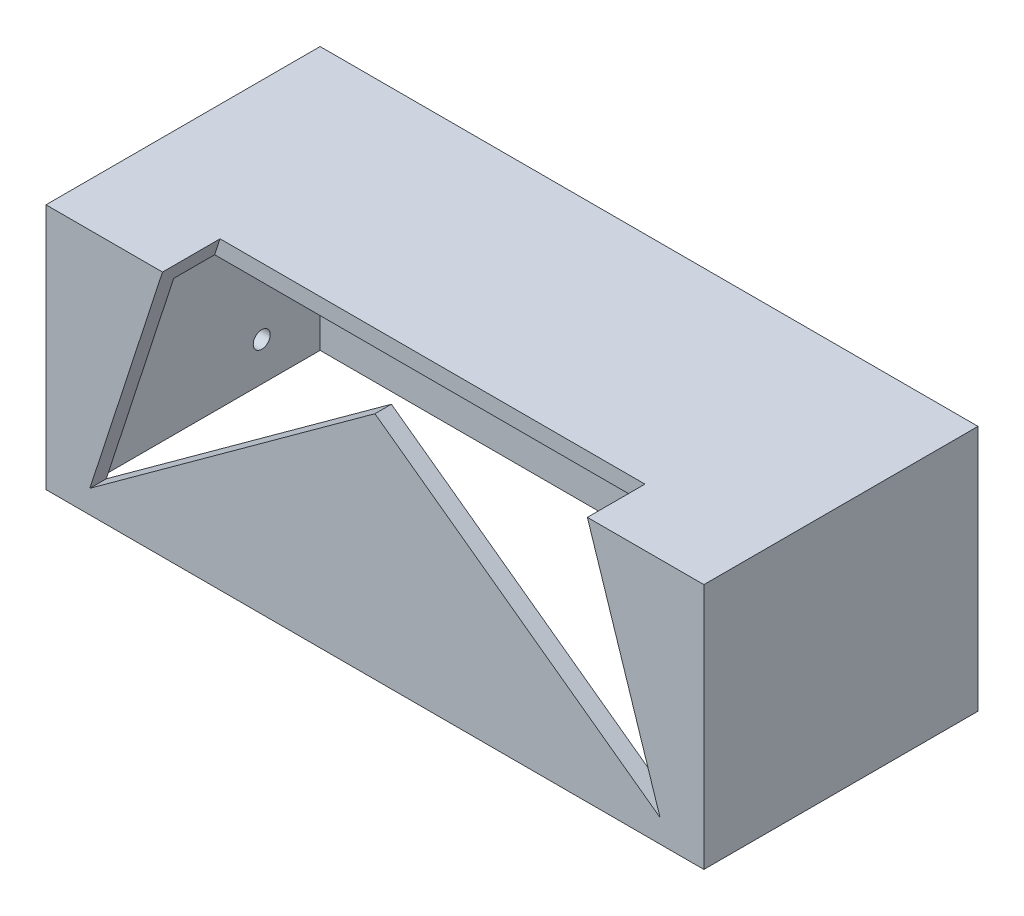
SolidWorks part; units mm, degrees
ref_plane "Alzado" through (0, 0, 0) normal (0, 0, 1) x (1, 0, 0)
ref_plane "Planta" through (0, 0, 0) normal (0, 1, 0) x (1, 0, 0)
ref_plane "Vista lateral" through (0, 0, 0) normal (1, 0, 0) x (0, 0, -1)
sketch "Croquis2" plane through (0, 0, -12) normal (0, 0, 1) x (1, 0, 0)
  line L0 (0, 0) -> (0, -53.289) construction
  line L2 (-60, -75.789) -> (60, -75.789)
  line L3 (-60, -75.789) -> (-60, -30.789)
  line L4 (-60, -30.789) -> (60, -30.789)
  line L5 (60, -75.789) -> (60, -30.789)
  line L6 (-60, -75.789) -> (60, -30.789) construction
  line L7 (-60, -30.789) -> (60, -75.789) construction
  dimension "D1" = 5
  dimension "D2" = 45
  dimension "D3" = 120
extrude "Saliente-Extruir1" add sketch "Croquis2" against normal blind 45 and the other way blind 5
shell "Vaciado1" thickness 3
sketch "Croquis3" plane through (0, 0, -7) normal (0, 0, 1) x (1, 0, 0)
  line L10 (0, 87.5) -> (-19.645, 27.039)
  line L11 (-19.645, 27.039) -> (-83.2174, 27.039)
  line L12 (-83.2174, 27.039) -> (-31.7862, -10.328)
  line L13 (-31.7862, -10.328) -> (-51.4312, -70.789)
  line L14 (-51.4312, -70.789) -> (0, -33.422)
  line L15 (0, -33.422) -> (51.4312, -70.789)
  line L16 (51.4312, -70.789) -> (31.7862, -10.328)
  line L17 (31.7862, -10.328) -> (83.2174, 27.039)
  line L18 (83.2174, 27.039) -> (19.645, 27.039)
  line L19 (19.645, 27.039) -> (0, 87.5)
  line L20 (0, 87.5) -> (-19.645, 27.039) construction
  line L21 (-19.645, 27.039) -> (-83.2174, 27.039) construction
  line L22 (-83.2174, 27.039) -> (-31.7862, -10.328) construction
  line L23 (-31.7862, -10.328) -> (-51.4312, -70.789) construction
  line L24 (-51.4312, -70.789) -> (0, -33.422) construction
  line L25 (0, -33.422) -> (51.4312, -70.789) construction
  line L26 (51.4312, -70.789) -> (31.7862, -10.328) construction
  line L27 (31.7862, -10.328) -> (83.2174, 27.039) construction
  line L28 (83.2174, 27.039) -> (19.645, 27.039) construction
  line L29 (19.645, 27.039) -> (0, 87.5) construction
  line L40 (0, 88.4708) -> (-19.8629, 27.339)
  line L41 (-19.8629, 27.339) -> (-84.1408, 27.339)
  line L42 (-84.1408, 27.339) -> (-32.1389, -10.4426)
  line L43 (-32.1389, -10.4426) -> (-52.0018, -71.5744)
  line L44 (-52.0018, -71.5744) -> (0, -33.7928)
  line L45 (0, -33.7928) -> (52.0018, -71.5744)
  line L46 (52.0018, -71.5744) -> (32.1389, -10.4426)
  line L47 (32.1389, -10.4426) -> (84.1408, 27.339)
  line L48 (84.1408, 27.339) -> (19.8629, 27.339)
  line L49 (19.8629, 27.339) -> (0, 88.4708)
  line L50 (0, 88.4708) -> (-19.8629, 27.339)
  line L51 (-19.8629, 27.339) -> (-84.1408, 27.339)
  line L52 (-84.1408, 27.339) -> (-32.1389, -10.4426)
  line L53 (-32.1389, -10.4426) -> (-52.0018, -71.5744)
  line L54 (-52.0018, -71.5744) -> (0, -33.7928)
  line L55 (0, -33.7928) -> (52.0018, -71.5744)
  line L56 (52.0018, -71.5744) -> (32.1389, -10.4426)
  line L57 (32.1389, -10.4426) -> (84.1408, 27.339)
  line L58 (84.1408, 27.339) -> (19.8629, 27.339)
  line L59 (19.8629, 27.339) -> (0, 88.4708)
  dimension "D1" = 0
  dimension "D2" = 0.3
extrude "Cortar-Extruir2" cut sketch "Croquis3" against normal up to surface (10.5 mm away)
sketch "Croquis4" plane through (-60, 0, 0) normal (-1, 0, 0) x (0, 0, 1)
  line L0 (-52.5, -43.7542) -> (-48.9, -43.7542) construction
  line L1 (-48.9, -43.7542) -> (-48.9, -46.8542) construction
  line L2 (-48.9, -46.8542) -> (-52.5, -46.8542) construction
  line L3 (-52.5, -46.8542) -> (-52.5, -43.7542) construction
  line L12 (-43.5, -46.8542) -> (-47, -46.8542) construction
  line L13 (-47, -46.8542) -> (-47, -43.7542) construction
  line L14 (-47, -43.7542) -> (-39.7, -43.7542) construction
  line L15 (-39.7, -43.7542) -> (-39.7, -62.7542) construction
  line L16 (-39.7, -62.7542) -> (-47, -62.7542) construction
  line L17 (-47, -62.7542) -> (-47, -59.6542) construction
  line L18 (-47, -59.6542) -> (-43.5, -59.6542) construction
  line L19 (-43.5, -59.6542) -> (-43.5, -46.8542) construction
  line L20 (-52.5, -43.7542) -> (-48.9, -43.7542) construction
  line L21 (-48.9, -43.7542) -> (-48.9, -46.8542) construction
  line L22 (-48.9, -46.8542) -> (-52.5, -46.8542) construction
  line L23 (-52.5, -46.8542) -> (-52.5, -43.7542) construction
  line L24 (-43.5, -46.8542) -> (-47, -46.8542) construction
  line L25 (-47, -46.8542) -> (-47, -43.7542) construction
  line L26 (-47, -43.7542) -> (-39.7, -43.7542) construction
  line L27 (-39.7, -43.7542) -> (-39.7, -62.7542) construction
  line L28 (-39.7, -62.7542) -> (-47, -62.7542) construction
  line L29 (-47, -62.7542) -> (-47, -59.6542) construction
  line L30 (-47, -59.6542) -> (-43.5, -59.6542) construction
  line L31 (-43.5, -59.6542) -> (-43.5, -46.8542) construction
  line L32 (-44.5, -53.2542) -> (-43.5, -53.2542) construction
  line L37 (-52.5, -58.5042) -> (-44.5, -58.5042)
  line L38 (-52.5, -58.5042) -> (-52.5, -48.0042)
  line L39 (-52.5, -48.0042) -> (-44.5, -48.0042)
  line L40 (-44.5, -58.5042) -> (-44.5, -48.0042)
  circle A0 centre (-43.35, -37.7716) radius 1.55 construction
  circle A1 centre (-43.35, -68.7368) radius 1.55 construction
  circle A2 centre (-43.35, -37.7716) radius 1.55
  circle A3 centre (-43.35, -68.7368) radius 1.55
  dimension "D2" = 10.5
  dimension "D4" = 1
extrude "Cortar-Extruir3" cut sketch "Croquis4" against normal up to next
sketch "Croquis5" plane through (0, 0, -57) normal (0, 0, -1) x (-1, 0, 0)
  circle A0 centre (7.6174, -53.2542) radius 1.55 construction
  circle A1 centre (7.6174, -53.2542) radius 1.55
extrude "Cortar-Extruir4" cut sketch "Croquis5" against normal up to next
